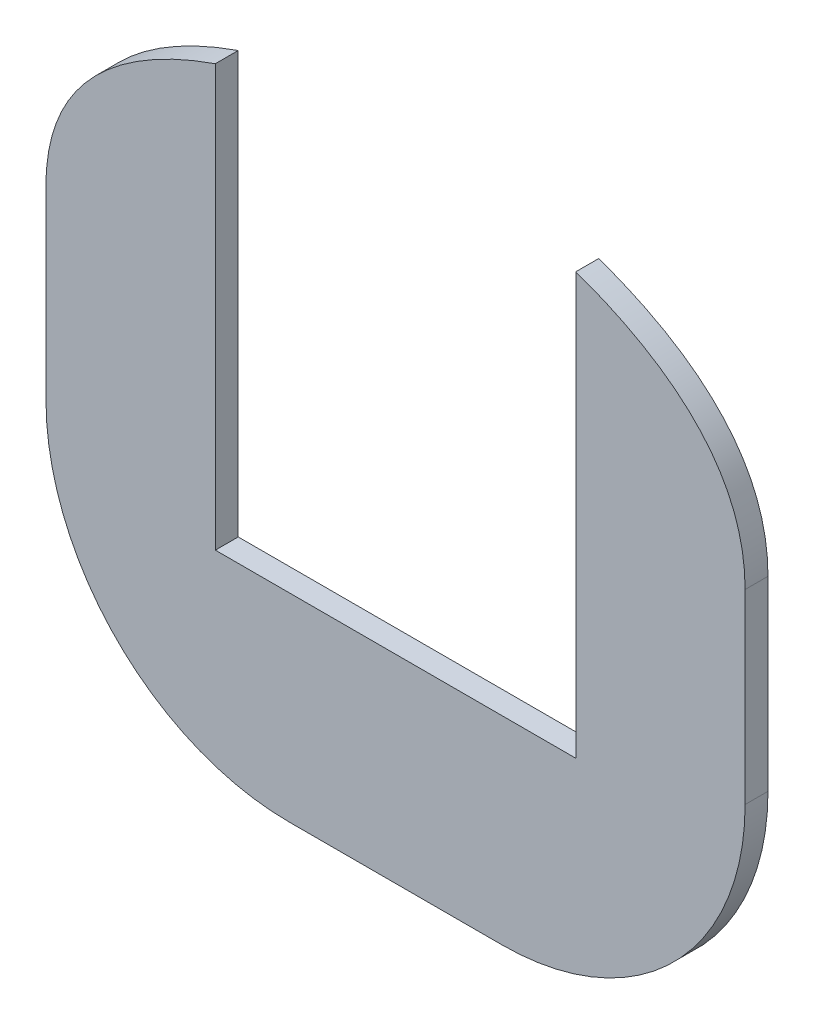
SolidWorks part; units mm, degrees
ref_plane "Front Plane" through (0, 0, 0) normal (0, 0, 1) x (1, 0, 0)
ref_plane "Top Plane" through (0, 0, 0) normal (0, 1, 0) x (1, 0, 0)
ref_plane "Right Plane" through (0, 0, 0) normal (1, 0, 0) x (0, 0, -1)
sketch "Sketch1" plane through (0, 0, 0) normal (0, 0, 1) x (1, 0, 0)
  line L0 (0, 33.5) -> (0, -96.5) construction
  line L1 (-70, 33.5) -> (70, 33.5) construction
  line L2 (-70, 33.5) -> (-70, -96.5) construction
  line L3 (-70, -96.5) -> (70, -96.5) construction
  line L4 (70, 33.5) -> (70, -96.5) construction
  line L5 (-25, 33.5) -> (25, 33.5) construction
  line L6 (-20, -96.5) -> (20, -96.5) construction
  line L7 (-70, -11.5) -> (70, -11.5) construction
  line L8 (-70, -11.5) -> (-70, -46.5) construction
  line L9 (-70, -46.5) -> (70, -46.5) construction
  line L10 (70, -11.5) -> (70, -46.5) construction
  line L11 (-10, 33.5) -> (10, 33.5) construction
  line L12 (-20, -96.5) -> (-14.4295, -96.5) construction
  line L13 (-14.4295, -96.5) -> (20, -96.5) construction
  line L14 (-70, -11.5) -> (-70, 26.5) construction
  line L15 (-70, 26.5) -> (-18, 33.5) construction
  line L16 (-18, 33.5) -> (-10, 33.5) construction
  line L17 (10, 33.5) -> (18, 33.5) construction
  line L18 (18, 33.5) -> (70, 26.5) construction
  line L19 (70, 26.5) -> (70, -11.5) construction
  line L20 (0, -55) -> (0, 55) construction
  line L21 (55, 0) -> (-55, 0) construction
  line L22 (-20, -92.2) -> (-14.4295, -92.2)
  line L23 (-14.4295, -92.2) -> (20, -92.2)
  line L24 (65.7, -11.5) -> (65.7, -46.5)
  line L25 (-10, 29.2) -> (10, 29.2)
  line L26 (-65.7, -11.5) -> (-65.7, -46.5)
  arc A0 (-70, -11.5) -> (-25, 33.5) centre (-25, -11.5) cw construction
  arc A1 (25, 33.5) -> (70, -11.5) centre (25, -11.5) cw construction
  arc A2 (-70, -46.5) -> (-20, -96.5) centre (-20, -46.5) ccw construction
  arc A3 (20, -96.5) -> (70, -46.5) centre (20, -46.5) ccw construction
  arc A4 (-65.7, -46.5) -> (-20, -92.2) centre (-20, -46.5) ccw
  arc A5 (20, -92.2) -> (65.7, -46.5) centre (20, -46.5) ccw
  spline S0 degree 3 poles (-70, -11.5) (-70, 26.5) (-18, 33.5) (-10, 33.5) knots 0 0 0 0 1 1 1 1 construction
  spline S1 degree 3 poles (10, 33.5) (18, 33.5) (70, 26.5) (70, -11.5) knots 0 0 0 0 1 1 1 1 construction
  spline S2 degree 1 poles (10, 29.2) (65.7, -11.5) knots 0 0 1 1 construction
  spline S3 degree 1 poles (-65.7, -11.5) (-10, 29.2) knots 0 0 1 1 construction
  spline S4 degree 3 poles (65.7, -11.5) (65.7, -10.9756) (65.6772, -9.9155) (65.5442, -7.8884) (65.2202, -5.4607) (64.5981, -2.7237) (63.4785, 0.7162) (61.5699, 4.6545) (58.5534, 8.8853) (54.8963, 12.6626) (49.3052, 17.1178) (41.2794, 21.6169) (32.8026, 24.7807) (26.3389, 26.6062) (21.7972, 27.6518) (17.7102, 28.4039) (14.8087, 28.8127) (12.8723, 29.0253) (11.6336, 29.1319) (10.8115, 29.1802) (10.283, 29.1976) (10.1012, 29.2) (10, 29.2) knots 0 0 0 0 0.015625 0.03125 0.0625 0.09375 0.125 0.1875 0.25 0.3125 0.375 0.5 0.625 0.6875 0.75 0.8125 0.875 0.90625 0.9375 0.96875 0.984375 1 1 1 1
  spline S5 degree 3 poles (-10, 29.2) (-10.1012, 29.2) (-10.283, 29.1976) (-10.8115, 29.1802) (-11.6336, 29.1319) (-12.8723, 29.0253) (-14.8087, 28.8127) (-17.7102, 28.4039) (-21.7972, 27.6518) (-26.3389, 26.6062) (-32.8026, 24.7807) (-41.2794, 21.6169) (-49.3052, 17.1178) (-54.8963, 12.6626) (-58.5534, 8.8853) (-61.5699, 4.6545) (-63.4785, 0.7162) (-64.5981, -2.7237) (-65.2202, -5.4607) (-65.5442, -7.8884) (-65.6772, -9.9155) (-65.7, -10.9756) (-65.7, -11.5) knots 0 0 0 0 0.015625 0.03125 0.0625 0.09375 0.125 0.1875 0.25 0.3125 0.375 0.5 0.625 0.6875 0.75 0.8125 0.875 0.90625 0.9375 0.96875 0.984375 1 1 1 1
  point P10 (0, 33.5)
  point P19 (0, -96.5)
  point P24 (0, 33.5)
  dimension "D3" = 50
  dimension "D1" = 130
  dimension "D2" = 140
  dimension "D4" = 20
  dimension "D5" = 45
  dimension "D6" = 38
  dimension "D7" = 52
  dimension "D8" = 52
  dimension "D9" = 38
  dimension "D10" = 11.5
  dimension "D11" = 4.3
extrude "Boss-Extrude1" add sketch "Sketch1" along normal blind 4.3
sketch "Sketch2" plane through (0, 0, 4.3) normal (0, 0, 1) x (1, 0, 0)
  line L0 (0, -2.365) -> (0, 2.365) construction
  line L1 (-33.87, 24.2997) -> (33.87, 24.2997) construction
  line L2 (-33.87, 24.2997) -> (-33.87, -54.8803)
  line L3 (-33.87, -54.8803) -> (33.87, -54.8803)
  line L4 (33.87, 24.2997) -> (33.87, -54.8803)
  line L6 (-33.87, 24.2997) -> (33.87, 24.2997) construction
  line L7 (-33.87, 24.2997) -> (-33.87, 35.4689)
  line L8 (-33.87, 35.4689) -> (33.87, 35.4689)
  line L9 (33.87, 24.2997) -> (33.87, 35.4689)
  spline S0 degree 3 poles (65.7, -11.5) (65.7, -10.9756) (65.6772, -9.9155) (65.5442, -7.8884) (65.2202, -5.4607) (64.5981, -2.7237) (63.4785, 0.7162) (61.5699, 4.6545) (58.5534, 8.8853) (54.8963, 12.6626) (49.3052, 17.1178) (41.2794, 21.6169) (32.8026, 24.7807) (26.3389, 26.6062) (21.7972, 27.6518) (17.7102, 28.4039) (14.8087, 28.8127) (12.8723, 29.0253) (11.6336, 29.1319) (10.8115, 29.1802) (10.283, 29.1976) (10.1012, 29.2) (10, 29.2) knots 0 0 0 0 0.015625 0.03125 0.0625 0.09375 0.125 0.1875 0.25 0.3125 0.375 0.5 0.625 0.6875 0.75 0.8125 0.875 0.90625 0.9375 0.96875 0.984375 1 1 1 1 construction
  point P4 (0, -54.8803)
  dimension "D1" = 67.74
  dimension "D2" = 79.18
extrude "Cut-Extrude1" cut sketch "Sketch2" against normal blind 10
